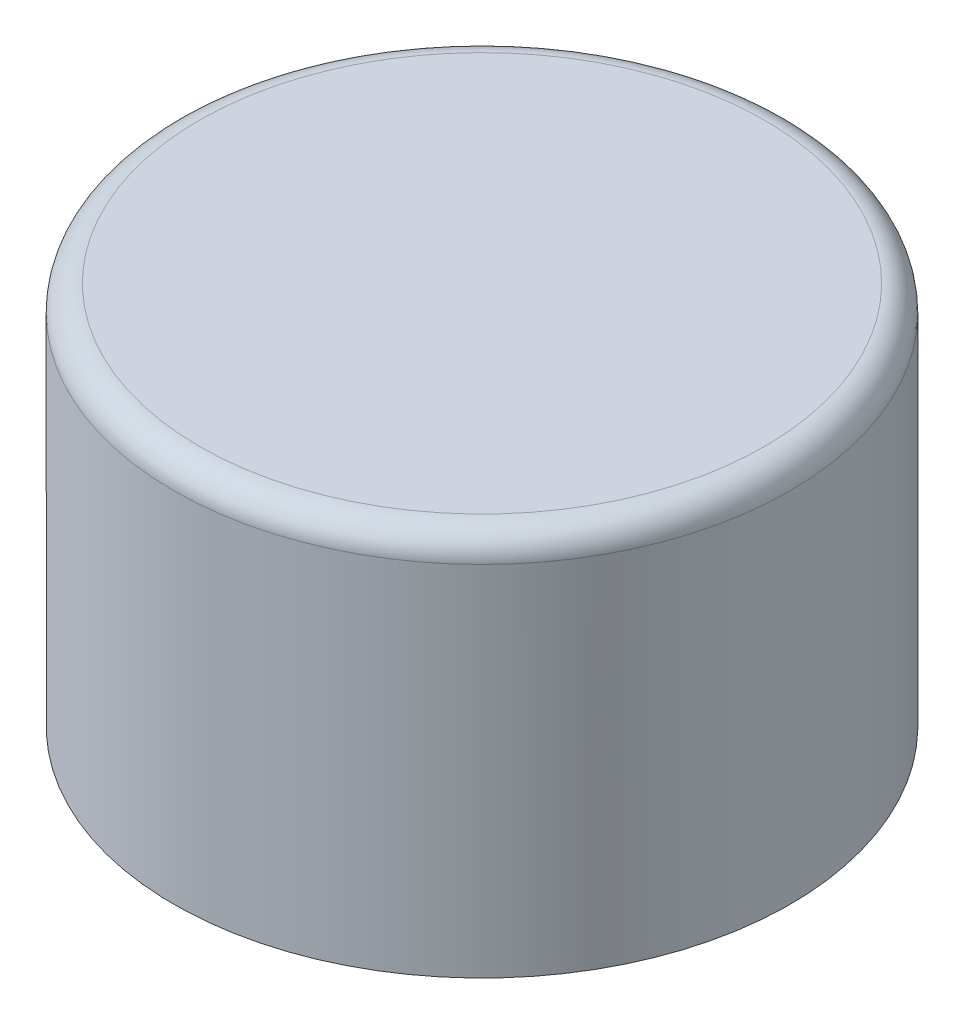
SolidWorks part; units mm, degrees
ref_plane "Front Plane" through (0, 0, 0) normal (0, 0, 1) x (1, 0, 0)
ref_plane "Top Plane" through (0, 0, 0) normal (0, 1, 0) x (1, 0, 0)
ref_plane "Right Plane" through (0, 0, 0) normal (1, 0, 0) x (0, 0, -1)
sketch "Sketch1" plane through (0, 0, 0) normal (0, 1, 0) x (1, 0, 0)
  circle A0 centre (0, 0) radius 30.5943
extrude "Boss-Extrude1" add sketch "Sketch1" along normal blind 38.1
shell "Shell1" thickness 0.254
fillet "Fillet1" radius 2.54 1 edges at (0, 37.846, 30.3403)
fillet "Fillet2" radius 2.54 1 edges at (0, 38.1, 30.5943)
